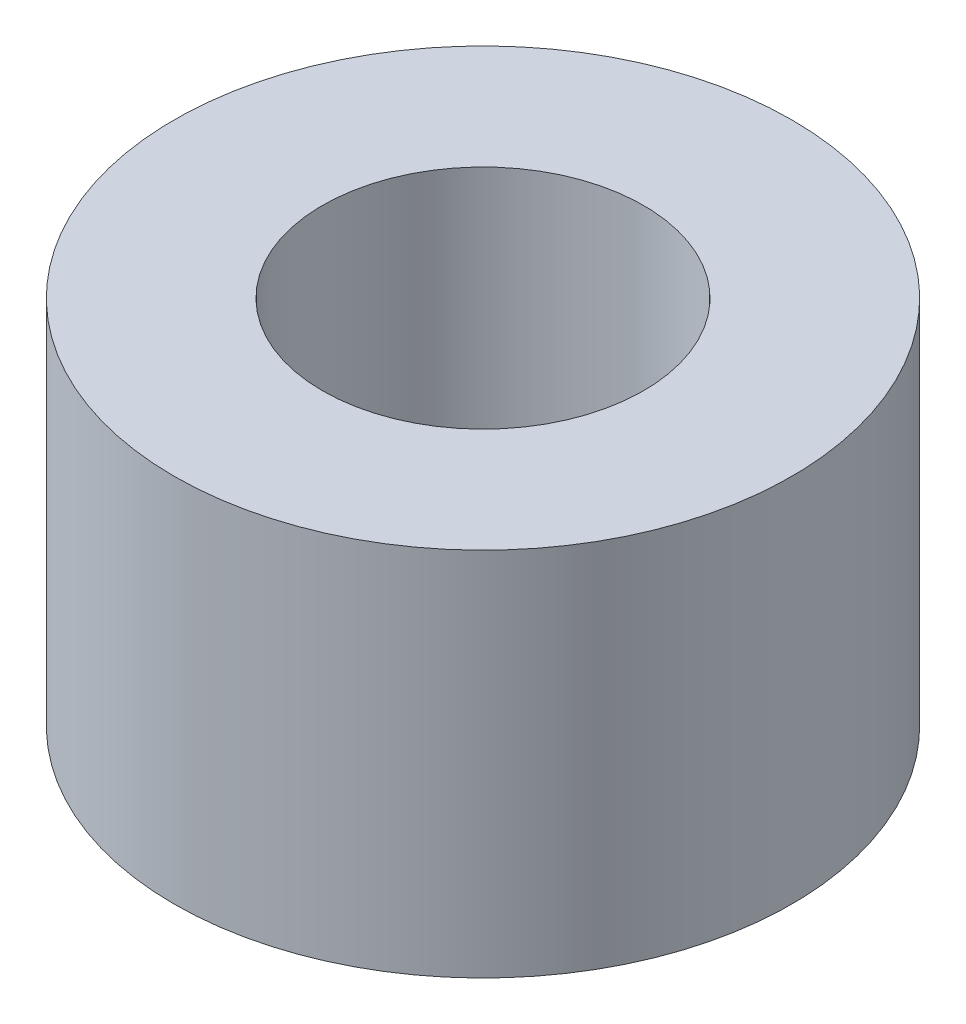
SolidWorks part; units mm, degrees
ref_plane "Face" through (0, 0, 0) normal (0, 0, 1) x (1, 0, 0)
ref_plane "Dessus" through (0, 0, 0) normal (0, 1, 0) x (1, 0, 0)
ref_plane "Droite" through (0, 0, 0) normal (1, 0, 0) x (0, 0, -1)
sketch "Esquisse1" plane through (0, 0, 0) normal (0, 1, 0) x (1, 0, 0)
  circle A0 centre (0, 0) radius 12.5
  circle A1 centre (0, 0) radius 6.5
  dimension "D1" = 25
  dimension "D2" = 13
extrude "Extrusion1" add sketch "Esquisse1" along normal blind 15
